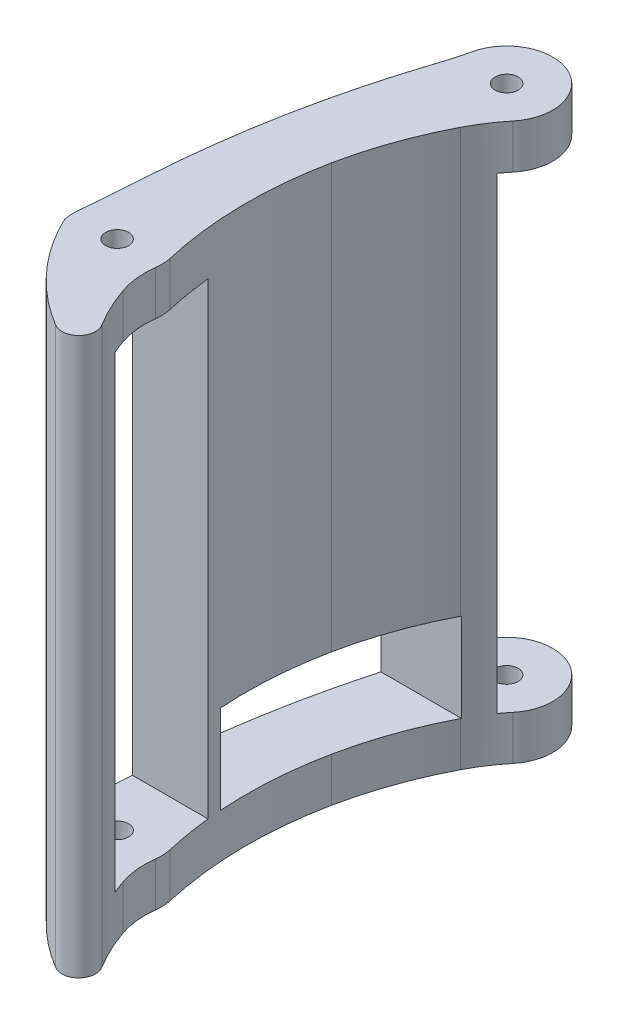
SolidWorks part; units mm, degrees
ref_plane "Front Plane" through (0, 0, 0) normal (0, 0, 1) x (1, 0, 0)
ref_plane "Top Plane" through (0, 0, 0) normal (0, 1, 0) x (1, 0, 0)
ref_plane "Right Plane" through (0, 0, 0) normal (1, 0, 0) x (0, 0, -1)
sketch "Sketch1" plane through (0, 0, 0) normal (0, 1, 0) x (1, 0, 0)
  line L0 (-49.2049, -37.6819) -> (-49.2049, -77.8139) construction
  line L1 (-49.2049, -37.6819) -> (45.278, -37.6819) construction
  line L2 (-26.8008, -20.9801) -> (-26.8008, -10.2995) construction
  arc A0 (-46.3471, -12.8206) -> (-45.6079, -3.1324) centre (-526.6294, 28.6968) ccw
  arc A1 (-33.7244, -14.1916) -> (-33.8317, -11.9466) centre (-40.0207, -13.3674) ccw
  arc A2 (-48.99, 25.5713) -> (-41.8324, 31.5556) centre (-47.886, 31.5234) ccw construction
  circle A3 centre (-31.3995, 33.846) radius 1.651
  arc A4 (-38.8468, 31.6213) -> (-45.6079, -3.1324) centre (94.8767, -12.4282) ccw
  arc A5 (-38.8468, 31.6213) -> (-37.8496, 35.2633) centre (-74.0509, 43.2178) ccw
  arc A6 (-29.2789, 25.1337) -> (-34.1177, 11.4284) centre (17.5666, 0.8875) ccw
  arc A7 (-33.1981, -19.3272) -> (-30.4429, -25.1461) centre (-4.9424, -9.5098) ccw
  arc A8 (-46.2307, -14.6933) -> (-33.7236, -28.4626) centre (-17.2547, -0.9384) ccw
  circle A9 centre (-40.0207, -13.3674) radius 1.651
  arc A10 (-33.7236, -28.4626) -> (-30.4429, -25.1461) centre (-32.4904, -26.4016) ccw
  arc A11 (-46.3471, -12.8206) -> (-46.2307, -14.6933) centre (-40.0207, -13.3674) ccw
  arc A12 (-26.3003, 29.6495) -> (-29.2789, 25.1337) centre (-6.465, 13.3257) ccw
  arc A14 (-34.1177, 11.4284) -> (-33.8317, -11.9466) centre (19.953, 0.4008) ccw
  arc A15 (-33.7244, -14.1916) -> (-33.1981, -19.3272) centre (-22.6061, -15.647) ccw
  arc A17 (-26.3003, 29.6495) -> (-37.8496, 35.2633) centre (-31.3995, 33.846) ccw
  dimension "D1" = 12.7
  dimension "D2" = 3.302
  dimension "D3" = 13.208
  dimension "D6" = 3.302
extrude "Boss-Extrude1" add sketch "Sketch1" along normal blind 79.756
ref_plane "Plane1" through (0, 6.35, 0) normal (0, 1, 0) x (-1, 0, 0)
sketch "Sketch3" plane through (0, 6.35, 0) normal (0, 1, 0) x (-1, 0, 0)
  line L0 (33.1924, 5.4358) -> (47.2859, 5.4358)
  line L1 (47.2859, 5.4358) -> (46.6329, 11.1161)
  line L2 (33.1924, 5.4358) -> (33.451, 10.9947)
  line L3 (30.1949, 21.1657) -> (44.6011, 21.1657)
  line L4 (30.1949, 21.1657) -> (33.0551, 12.8473)
  line L5 (44.6011, 21.1657) -> (46.3166, 16.3925)
  circle A0 centre (31.3995, -33.846) radius 6.858
  arc A1 (33.0551, 12.8473) -> (33.451, 10.9947) centre (40.0207, 13.3674) ccw
  arc A2 (46.6329, 11.1161) -> (46.3166, 16.3925) centre (40.0207, 13.3674) ccw
  dimension "D1" = 13.716
  dimension "D2" = 13.97
extrude "Cut-Extrude2" cut sketch "Sketch3" along normal blind 67.056
sketch "Sketch4" plane through (0, 6.35, 0) normal (0, 1, 0) x (-1, 0, 0)
  line L0 (28.4555, -25.2067) -> (46.0631, -25.2067)
  line L1 (46.0631, -25.2067) -> (52.8622, 3.477)
  line L2 (52.8622, 3.477) -> (29.7303, 3.477)
  line L3 (29.7303, 3.477) -> (28.4555, -25.2067)
extrude "Cut-Extrude3" cut sketch "Sketch4" along normal blind 12.7
